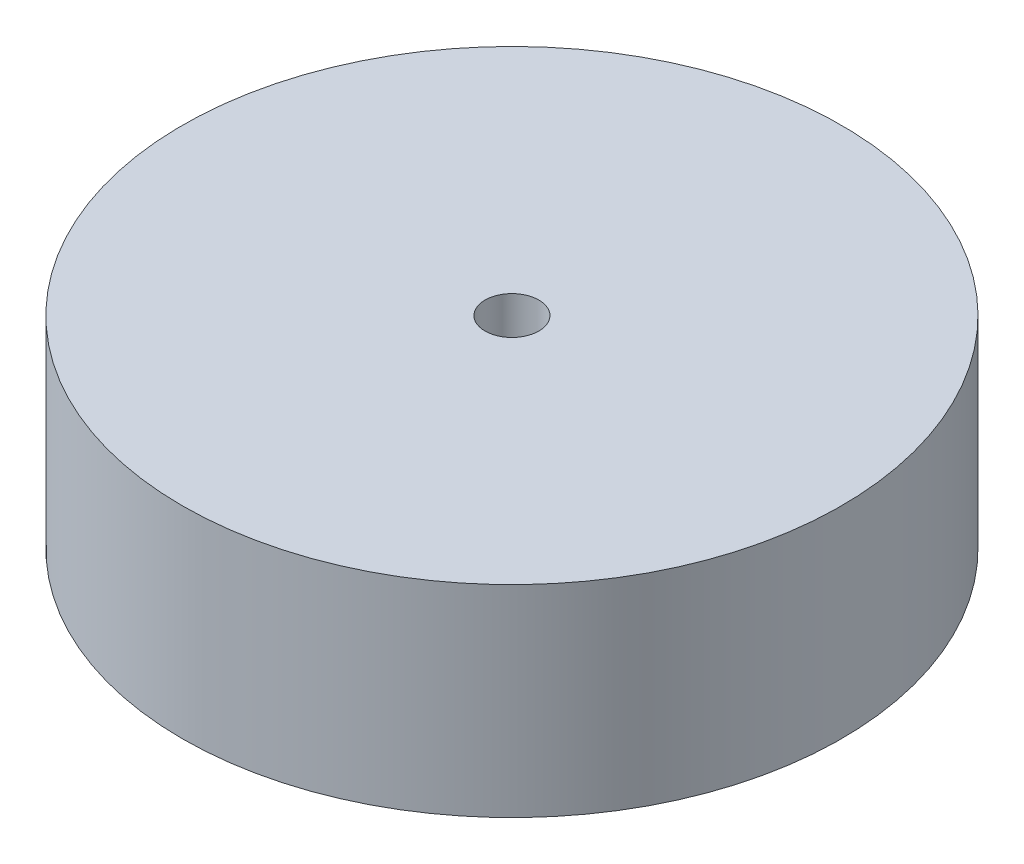
SolidWorks part; units mm, degrees
ref_plane "Front Plane" through (0, 0, 0) normal (0, 0, 1) x (1, 0, 0)
ref_plane "Top Plane" through (0, 0, 0) normal (0, 1, 0) x (1, 0, 0)
ref_plane "Right Plane" through (0, 0, 0) normal (1, 0, 0) x (0, 0, -1)
sketch "Sketch1" plane through (0, 0, 0) normal (0, 1, 0) x (1, 0, 0)
  circle A0 centre (0, 0) radius 24.5
extrude "Boss-Extrude1" add sketch "Sketch1" along normal blind 15
sketch "Sketch2" plane through (0, 0, 0) normal (0, 1, 0) x (1, 0, 0)
  circle A0 centre (0, 0) radius 2
extrude "Cut-Extrude1" cut sketch "Sketch2" against normal through all and the other way through all
